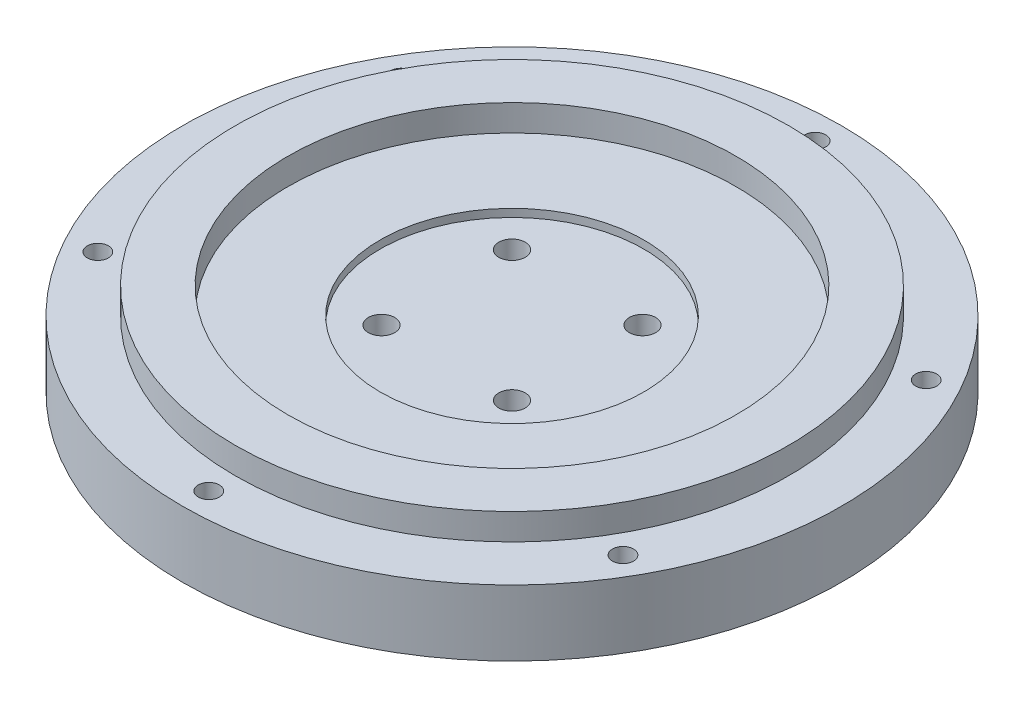
SolidWorks part; units mm, degrees
ref_plane "Front Plane" through (0, 0, 0) normal (0, 0, 1) x (1, 0, 0)
ref_plane "Top Plane" through (0, 0, 0) normal (0, 1, 0) x (1, 0, 0)
ref_plane "Right Plane" through (0, 0, 0) normal (1, 0, 0) x (0, 0, -1)
sketch "Sketch1" plane through (0, 0, 0) normal (0, 1, 0) x (1, 0, 0)
  circle A0 centre (0, 0) radius 125
  circle A1 centre (0, 115) radius 4
  circle A16 centre (99.5929, 57.5) radius 4
  circle A17 centre (99.5929, -57.5) radius 4
  circle A18 centre (0, -115) radius 4
  circle A19 centre (-99.5929, -57.5) radius 4
  circle A20 centre (-99.5929, 57.5) radius 4
  point P16 (0, 0)
  point P17 (0, 0)
  point P31 (0, 0)
  point P36 (0, 0)
  dimension "D1" = 250
  dimension "D2" = 8
  dimension "D3" = 115
  dimension "D6" = 6
extrude "Boss-Extrude1" add sketch "Sketch1" along normal blind 25
sketch "Sketch3" plane through (0, 25, 0) normal (0, 1, 0) x (1, 0, 0)
  circle A0 centre (0, 0) radius 50
  dimension "D1" = 100
sketch "Sketch4" plane through (0, 0, 0) normal (0, -1, 0) x (1, 0, 0)
  line L1 (-24.7487, -24.7487) -> (24.7487, -24.7487) construction
  line L2 (-24.7487, -24.7487) -> (-24.7487, 24.7487) construction
  line L3 (-24.7487, 24.7487) -> (24.7487, 24.7487) construction
  line L4 (24.7487, -24.7487) -> (24.7487, 24.7487) construction
  line L5 (-24.7487, -24.7487) -> (24.7487, 24.7487) construction
  line L6 (-24.7487, 24.7487) -> (24.7487, -24.7487) construction
  circle A0 centre (-24.7487, 24.7487) radius 9
  circle A1 centre (24.7487, 24.7487) radius 9
  circle A2 centre (24.7487, -24.7487) radius 9
  circle A3 centre (-24.7487, -24.7487) radius 9
  point P0 (0, 0)
  dimension "D2" = 18
  dimension "D1" = 70
extrude "Cut-Extrude1" cut sketch "Sketch4" against normal blind 10
sketch "Sketch6" plane through (0, 10, 0) normal (0, -1, 0) x (1, 0, 0)
  circle A0 centre (-24.7487, 24.7487) radius 5
  circle A1 centre (24.7487, 24.7487) radius 5
  circle A2 centre (24.7487, -24.7487) radius 5
  circle A3 centre (-24.7487, -24.7487) radius 5
  dimension "D1" = 10
extrude "Cut-Extrude2" cut sketch "Sketch6" against normal up to surface (15 mm away) up to face at (-99.5929, 25, 61.5)
sketch "Sketch7" plane through (0, 25, 0) normal (0, 1, 0) x (1, 0, 0)
  circle A0 centre (0, 0) radius 50
  dimension "D1" = 100
extrude "Cut-Extrude3" cut sketch "Sketch7" against normal blind 3
sketch "Sketch8" plane through (0, 25, 0) normal (0, 1, 0) x (1, 0, 0)
  circle A0 centre (0, 0) radius 85
  circle A1 centre (0, 0) radius 105
  dimension "D1" = 170
  dimension "D2" = 20
extrude "Boss-Extrude2" add sketch "Sketch8" along normal blind 10
